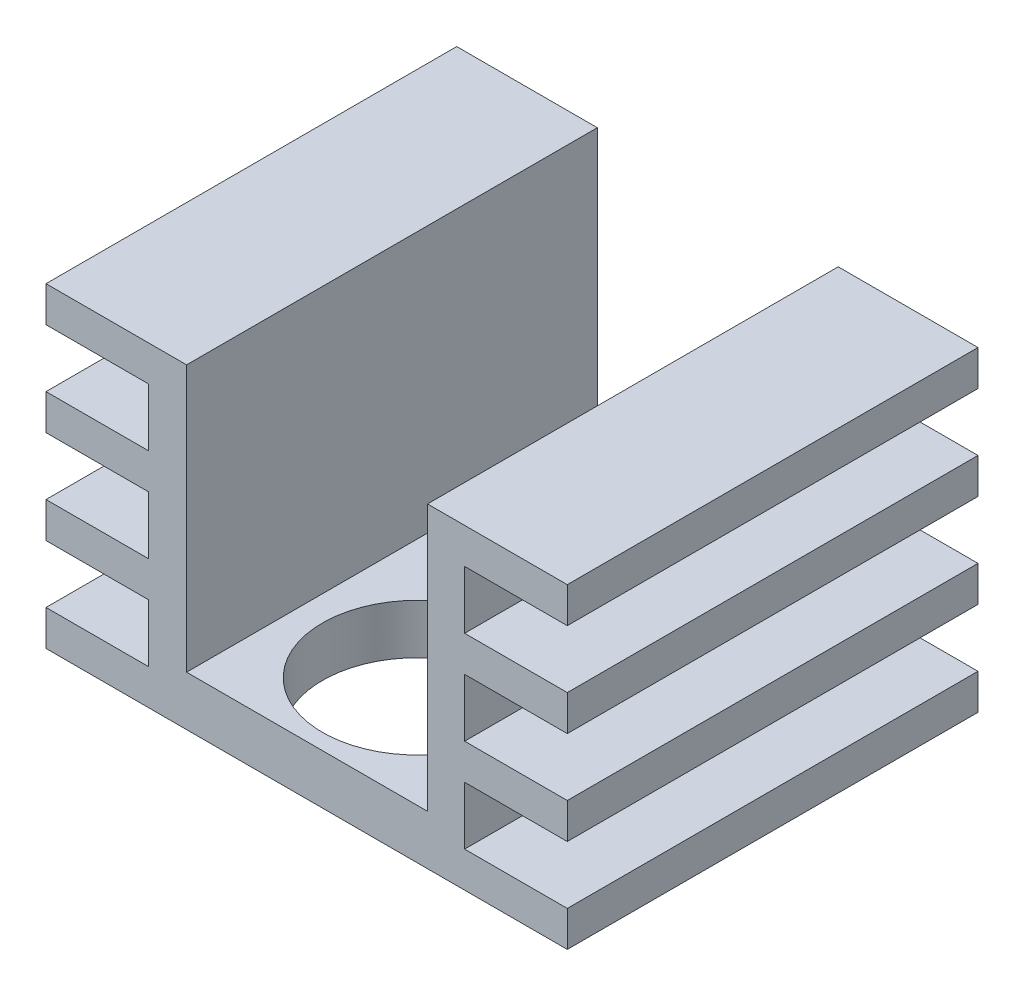
SolidWorks part; units mm, degrees
ref_plane "Front Plane" through (0, 0, 0) normal (0, 0, 1) x (1, 0, 0)
ref_plane "Top Plane" through (0, 0, 0) normal (0, 1, 0) x (1, 0, 0)
ref_plane "Right Plane" through (0, 0, 0) normal (1, 0, 0) x (0, 0, -1)
sketch "Sketch1" plane through (0, 0, 0) normal (0, 1, 0) x (1, 0, 0)
  line L0 (0, 0) -> (0, 26)
  line L1 (0, 26) -> (33, 26)
  line L2 (33, 26) -> (33, 0)
  line L3 (33, 0) -> (0, 0)
  circle A0 centre (16.5, 7) radius 6
  dimension "D1" = 26
  dimension "D5" = 12
  dimension "D2" = 33
  dimension "D3" = 7
  dimension "D4" = 16.5
extrude "Boss-Extrude1" add sketch "Sketch1" along normal blind 20
sketch "Sketch2" plane through (0, 0, 0) normal (0, 0, 1) x (1, 0, 0)
  line L1 (0, 2.25) -> (6.5, 2.25)
  line L2 (0, 5.9167) -> (0, 2.25)
  line L3 (0, 5.9167) -> (6.5, 5.9167)
  line L4 (6.5, 2.25) -> (6.5, 5.9167)
  line L5 (0, 20) -> (0, 0) construction
  line L6 (0, 8.1667) -> (6.5, 8.1667)
  line L7 (0, 8.1667) -> (0, 11.8333)
  line L8 (0, 11.8333) -> (6.5, 11.8333)
  line L9 (6.5, 8.1667) -> (6.5, 11.8333)
  line L10 (33, 20) -> (33, 0) construction
  line L11 (0, 17.75) -> (6.5, 17.75)
  line L12 (0, 17.75) -> (0, 14.0833)
  line L13 (0, 14.0833) -> (6.5, 14.0833)
  line L14 (6.5, 17.75) -> (6.5, 14.0833)
  line L15 (33, 17.75) -> (26.5, 17.75)
  line L16 (33, 17.75) -> (33, 14.0833)
  line L17 (33, 14.0833) -> (26.5, 14.0833)
  line L18 (26.5, 17.75) -> (26.5, 14.0833)
  line L19 (33, 11.8333) -> (26.5, 11.8333)
  line L20 (33, 11.8333) -> (33, 8.1667)
  line L21 (33, 8.1667) -> (26.5, 8.1667)
  line L22 (26.5, 11.8333) -> (26.5, 8.1667)
  line L23 (33, 5.9167) -> (26.5, 5.9167)
  line L24 (33, 5.9167) -> (33, 2.25)
  line L25 (33, 2.25) -> (26.5, 2.25)
  line L26 (26.5, 5.9167) -> (26.5, 2.25)
  line L28 (0, 20) -> (33, 20) construction
  line L29 (0, 0) -> (33, 0) construction
  line L31 (8.9, 20) -> (24.15, 20)
  line L32 (8.9, 20) -> (8.9, 3.15)
  line L33 (8.9, 3.15) -> (24.15, 3.15)
  line L34 (24.15, 20) -> (24.15, 3.15)
  dimension "D1" = 2.25
  dimension "D2" = 2.25
  dimension "D3" = 2.25
  dimension "D4" = 2.25
  dimension "D5" = 6.5
  dimension "D6" = 2.25
  dimension "D7" = 2.25
  dimension "D8" = 2.25
  dimension "D9" = 15.25
  dimension "D10" = 3.15
  dimension "D11" = 2.4
extrude "Cut-Extrude1" cut sketch "Sketch2" against normal blind 26
